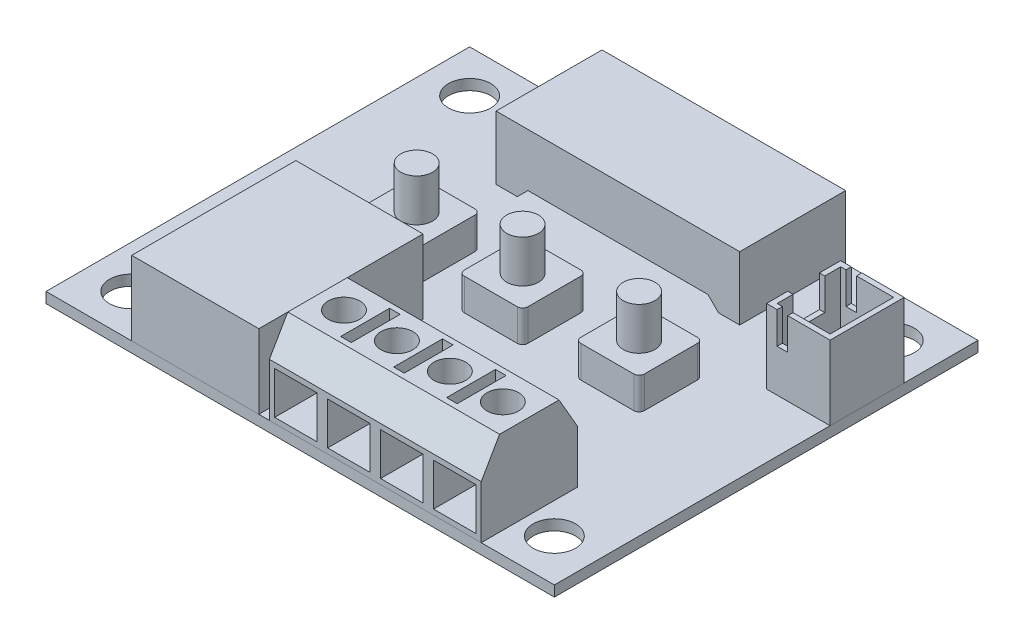
SolidWorks part; units mm, degrees
ref_plane "Front Plane" through (0, 0, 0) normal (0, 0, 1) x (1, 0, 0)
ref_plane "Top Plane" through (0, 0, 0) normal (0, 1, 0) x (1, 0, 0)
ref_plane "Right Plane" through (0, 0, 0) normal (1, 0, 0) x (0, 0, -1)
sketch "Sketch1" plane through (0, 0, 0) normal (0, 1, 0) x (1, 0, 0)
  line L1 (-24, -20) -> (24, -20)
  line L2 (-24, -20) -> (-24, 20)
  line L3 (-24, 20) -> (24, 20)
  line L4 (24, -20) -> (24, 20)
  line L5 (-24, -20) -> (24, 20) construction
  line L6 (-24, 20) -> (24, -20) construction
  point P0 (0, 0)
  dimension "D1" = 48
  dimension "D2" = 40
extrude "Boss-Extrude1" add sketch "Sketch1" along normal blind 1
sketch "Sketch2" plane through (0, 0, 0) normal (0, -1, 0) x (1, 0, 0)
  line L8 (14, -10) -> (14, 10)
  line L9 (14, 10) -> (-14, 10)
  line L10 (-14, 10) -> (-14, -10)
  line L11 (-14, -10) -> (14, -10)
  line L12 (14, -10) -> (14, 10)
  line L13 (14, 10) -> (-14, 10)
  line L14 (-14, 10) -> (-14, -10)
  line L15 (-14, -10) -> (14, -10)
  dimension "D1" = 10
extrude "Boss-Extrude2" add sketch "Sketch2" along normal blind 2
sketch "Sketch3" plane through (0, 1, 0) normal (0, 1, 0) x (1, 0, 0)
  line L6 (20, -16) -> (24, -16) construction
  line L7 (24, -20) -> (24, 20) construction
  line L8 (20, -16) -> (20, -20) construction
  line L9 (-24, -20) -> (24, -20) construction
  line L10 (-20, 16) -> (-20, 20) construction
  line L11 (24, 20) -> (-24, 20) construction
  line L12 (-20, 16) -> (-24, 16) construction
  line L13 (-24, 20) -> (-24, -20) construction
  circle A0 centre (-20, -16) radius 2
  circle A1 centre (20, -16) radius 2
  circle A2 centre (20, 16) radius 2
  circle A3 centre (-20, 16) radius 2
  dimension "D1" = 4
  dimension "D2" = 4
extrude "Cut-Extrude1" cut sketch "Sketch3" against normal through all
sketch "Sketch4" plane through (0, 1, 0) normal (0, 1, 0) x (1, 0, 0)
  line L0 (24, 20) -> (-24, 20) construction
  line L1 (-11.5, 10) -> (11.5, 10)
  line L2 (-11.5, 10) -> (-11.5, 20)
  line L3 (-11.5, 20) -> (11.5, 20)
  line L4 (11.5, 10) -> (11.5, 20)
  line L5 (-11.5, 10) -> (11.5, 20) construction
  line L6 (-11.5, 20) -> (11.5, 10) construction
  point P0 (0, 15)
  dimension "D1" = 23
  dimension "D2" = 10
extrude "Boss-Extrude3" add sketch "Sketch4" along normal blind 6 separate body
sketch "Sketch5" plane through (0, 1, 0) normal (0, 1, 0) x (1, 0, 0)
  line L0 (24, -20) -> (24, 20) construction
  line L1 (18, 13.0336) -> (24, 13.0336)
  line L2 (18, 13.0336) -> (18, 6.0336)
  line L3 (18, 6.0336) -> (24, 6.0336)
  line L4 (24, 13.0336) -> (24, 6.0336)
  line L5 (18, 13.0336) -> (24, 6.0336) construction
  line L6 (18, 6.0336) -> (24, 13.0336) construction
  point P0 (21, 9.5336)
  dimension "D1" = 7
  dimension "D2" = 6
extrude "Boss-Extrude4" add sketch "Sketch5" along normal blind 7 separate body
shell "Shell1" thickness 0.5
sketch "Sketch6" plane through (0, 8, 0) normal (0, 1, 0) x (1, 0, 0)
  line L0 (23.5, 12.5336) -> (18.5, 12.5336) construction
  line L7 (19, 13.0336) -> (20, 13.0336)
  line L14 (18.5, 12.5336) -> (18.5, 6.5336) construction
  line L15 (18, 8.0336) -> (18.5, 8.0336)
  line L16 (18, 8.0336) -> (18, 11.0336)
  line L17 (18, 11.0336) -> (18.5, 11.0336)
  line L18 (18.5, 8.0336) -> (18.5, 11.0336)
  line L19 (18, 8.0336) -> (18.5, 11.0336) construction
  line L20 (18, 11.0336) -> (18.5, 8.0336) construction
  line L21 (18, 13.0336) -> (18, 6.0336) construction
  line L22 (19, 13.0336) -> (19, 12.5336)
  line L23 (19, 12.5336) -> (20, 12.5336)
  line L24 (18.5, 12.5336) -> (18.5, 6.5336) construction
  line L33 (20, 13.0336) -> (20, 12.5336)
  line L34 (23.5, 12.5336) -> (18.5, 12.5336) construction
  line L35 (24, 13.0336) -> (18, 13.0336) construction
  line L36 (18.5, 6.5336) -> (23.5, 6.5336) construction
  line L37 (19, 6.5336) -> (20, 6.5336)
  line L38 (19, 6.5336) -> (19, 6.0336)
  line L39 (19, 6.0336) -> (20, 6.0336)
  line L40 (20, 6.5336) -> (20, 6.0336)
  line L41 (18, 6.0336) -> (24, 6.0336) construction
  point P14 (18.25, 9.5336)
  point P32 (18.5, 9.5336)
  dimension "D1" = 3
  dimension "D2" = 1
  dimension "D3" = 1
extrude "Cut-Extrude2" cut sketch "Sketch6" against normal blind 3
sketch "Sketch7" plane through (0, 0, -10) normal (0, 0, 1) x (1, 0, 0)
  line L0 (-11.5, 1) -> (11.5, 1) construction
  line L1 (-9.5, 1) -> (9.5, 1)
  line L3 (-8.5, 2) -> (8.5, 2)
  line L7 (9.5, 1) -> (8.5, 2)
  line L8 (-9.5, 1) -> (-8.5, 2)
  line L9 (-11.5, 7) -> (-11.5, 1) construction
  line L10 (11.5, 7) -> (11.5, 1) construction
  dimension "D1" = 1
  dimension "D2" = 45
  dimension "D3" = 2
  dimension "D4" = 2
extrude "Cut-Extrude3" cut sketch "Sketch7" against normal through all
sketch "Sketch8" plane through (0, 1, 0) normal (0, 1, 0) x (1, 0, 0)
  line L0 (-24, -20) -> (24, -20) construction
  line L1 (-15.9054, -20) -> (-3.9054, -20)
  line L2 (-15.9054, -20) -> (-15.9054, -4.5)
  line L3 (-15.9054, -4.5) -> (-3.9054, -4.5)
  line L4 (-3.9054, -20) -> (-3.9054, -4.5)
  dimension "D1" = 15.5
  dimension "D2" = 12
extrude "Boss-Extrude5" add sketch "Sketch8" along normal through all separate body
sketch "Sketch9" plane through (0, 1, 0) normal (0, 1, 0) x (1, 0, 0)
  line L0 (-24, -20) -> (24, -20) construction
  line L1 (-2.9054, -20) -> (17.0946, -20)
  line L2 (-2.9054, -20) -> (-2.9054, -10.9229)
  line L3 (-2.9054, -10.9229) -> (17.0946, -10.9229)
  line L4 (17.0946, -20) -> (17.0946, -10.9229)
  line L8 (-3.9054, -20) -> (-3.9054, -4.5) construction
  dimension "D1" = 20
  dimension "D2" = 1
extrude "Boss-Extrude6" add sketch "Sketch9" along normal blind 8 separate body
chamfer "Chamfer1" distance 3 angle 30 2 edges at (7.0946, 9, 10.9229) (7.0946, 9, 20)
sketch "Sketch10" plane through (0, 0, 20) normal (0, 0, 1) x (1, 0, 0)
  line L0 (17.0946, 6) -> (17.0946, 1) construction
  line L1 (16.5946, 1.5) -> (12.5946, 1.5)
  line L2 (16.5946, 1.5) -> (16.5946, 5.5)
  line L3 (16.5946, 5.5) -> (12.5946, 5.5)
  line L4 (12.5946, 1.5) -> (12.5946, 5.5)
  line L6 (17.0946, 6) -> (-2.9054, 6) construction
  line L7 (-2.9054, 1) -> (17.0946, 1) construction
  line L8 (11.5946, 1.5) -> (11.5946, 5.5)
  line L9 (11.5946, 1.5) -> (7.5946, 1.5)
  line L10 (7.5946, 1.5) -> (7.5946, 5.5)
  line L11 (11.5946, 5.5) -> (7.5946, 5.5)
  line L12 (6.5946, 1.5) -> (6.5946, 5.5)
  line L13 (6.5946, 1.5) -> (2.5946, 1.5)
  line L14 (2.5946, 1.5) -> (2.5946, 5.5)
  line L15 (6.5946, 5.5) -> (2.5946, 5.5)
  line L16 (1.5946, 1.5) -> (1.5946, 5.5)
  line L17 (1.5946, 1.5) -> (-2.4054, 1.5)
  line L18 (-2.4054, 1.5) -> (-2.4054, 5.5)
  line L19 (1.5946, 5.5) -> (-2.4054, 5.5)
  line L21 (-2.9054, 6) -> (-2.9054, 1) construction
  dimension "D1" = 0.5
  dimension "D2" = 0.5
  dimension "D3" = 0.5
  dimension "D4" = 4
  dimension "D6" = 0.5
  dimension "D5" = 4
extrude "Cut-Extrude4" cut sketch "Sketch10" against normal blind 5
sketch "Sketch11" plane through (0, 9, 0) normal (0, 1, 0) x (1, 0, 0)
  line L0 (16.5946, -20) -> (12.5946, -20) construction
  line L2 (11.5946, -17.7679) -> (12.5946, -17.7679)
  line L3 (11.5946, -17.7679) -> (11.5946, -13.155)
  line L4 (11.5946, -13.155) -> (12.5946, -13.155)
  line L5 (12.5946, -17.7679) -> (12.5946, -13.155)
  line L6 (1.5946, -20) -> (-2.4054, -20) construction
  line L7 (17.0946, -18.2679) -> (17.0946, -12.655) construction
  line L8 (6.5946, -17.7679) -> (6.5946, -13.155)
  line L9 (6.5946, -17.7679) -> (7.5946, -17.7679)
  line L10 (7.5946, -17.7679) -> (7.5946, -13.155)
  line L11 (6.5946, -13.155) -> (7.5946, -13.155)
  line L12 (1.5946, -17.7679) -> (1.5946, -13.155)
  line L13 (1.5946, -17.7679) -> (2.5946, -17.7679)
  line L14 (2.5946, -17.7679) -> (2.5946, -13.155)
  line L15 (1.5946, -13.155) -> (2.5946, -13.155)
  line L16 (-2.9054, -18.2679) -> (17.0946, -18.2679) construction
  circle A0 centre (14.5946, -15.4615) radius 1.5
  circle A1 centre (9.5946, -15.4615) radius 1.5
  circle A2 centre (4.5946, -15.4615) radius 1.5
  circle A3 centre (-0.4054, -15.4615) radius 1.5
  point P4 (14.5946, -20)
  point P15 (12.5946, -15.4615)
  point P21 (-0.4054, -20)
  point P24 (17.0946, -15.4615)
  dimension "D1" = 3
  dimension "D2" = 4
  dimension "D4" = 0.5
  dimension "D3" = 3
extrude "Cut-Extrude5" cut sketch "Sketch11" against normal blind 3
sketch "Sketch12" plane through (0, 1, 0) normal (0, 1, 0) x (1, 0, 0)
  line L0 (-24, -20) -> (24, -20) construction
  line L1 (-2.5, 4) -> (2.5, 4)
  line L2 (-3, 3.5) -> (-3, -1.5)
  line L3 (-2.5, -2) -> (2.5, -2)
  line L4 (3, 3.5) -> (3, -1.5)
  line L5 (-13, 3.5) -> (-13, -1.5)
  line L6 (-12.5, 4) -> (-7.5, 4)
  line L7 (-7, 3.5) -> (-7, -1.5)
  line L8 (-12.5, -2) -> (-7.5, -2)
  line L9 (-24, 20) -> (-24, -20) construction
  line L10 (8, 3.5) -> (8, -1.5)
  line L11 (8.5, 4) -> (13.5, 4)
  line L12 (14, 3.5) -> (14, -1.5)
  line L13 (8.5, -2) -> (13.5, -2)
  line L14 (24, -20) -> (24, 20) construction
  arc A0 (2.5, 4) -> (3, 3.5) centre (2.5, 3.5) cw
  arc A1 (-3, -1.5) -> (-2.5, -2) centre (-2.5, -1.5) ccw
  arc A2 (2.5, -2) -> (3, -1.5) centre (2.5, -1.5) ccw
  arc A3 (-2.5, 4) -> (-3, 3.5) centre (-2.5, 3.5) ccw
  arc A4 (-12.5, 4) -> (-13, 3.5) centre (-12.5, 3.5) ccw
  arc A5 (-13, -1.5) -> (-12.5, -2) centre (-12.5, -1.5) ccw
  arc A6 (-7.5, 4) -> (-7, 3.5) centre (-7.5, 3.5) cw
  arc A7 (-7.5, -2) -> (-7, -1.5) centre (-7.5, -1.5) ccw
  arc A8 (8.5, 4) -> (8, 3.5) centre (8.5, 3.5) ccw
  arc A9 (8, -1.5) -> (8.5, -2) centre (8.5, -1.5) ccw
  arc A10 (13.5, 4) -> (14, 3.5) centre (13.5, 3.5) cw
  arc A11 (13.5, -2) -> (14, -1.5) centre (13.5, -1.5) ccw
  point P12 (0, 4)
  dimension "D1" = 0.5
  dimension "D2" = 6
  dimension "D3" = 6
  dimension "D4" = 18
  dimension "D6" = 11
  dimension "D8" = 10
  dimension "D5" = 2
  dimension "D7" = 2
extrude "Boss-Extrude7" add sketch "Sketch12" along normal blind 3 separate body
sketch "Sketch13" plane through (0, 4, 0) normal (0, 1, 0) x (1, 0, 0)
  line L0 (2.5, 4) -> (-2.5, 4) construction
  line L1 (-3, 3.5) -> (-3, -1.5) construction
  line L2 (13.5, 4) -> (8.5, 4) construction
  line L3 (-7.5, 4) -> (-12.5, 4) construction
  circle A0 centre (0, 1) radius 1.5
  circle A1 centre (11, 1) radius 1.5
  circle A2 centre (-10, 1) radius 1.5
  point P4 (0, 4)
  point P8 (-3, 1)
  point P16 (11, 4)
  point P20 (-10, 4)
  dimension "D1" = 3
extrude "Boss-Extrude8" add sketch "Sketch13" along normal blind 4
equation "\"D6@Sketch10\"=\"D1@Sketch10\""
equation "\"D3@Sketch10\"=\"D1@Sketch10\""
equation "\"D2@Sketch10\"=\"D1@Sketch10\""
equation "\"D3@Sketch12\"=\"D2@Sketch12\""
